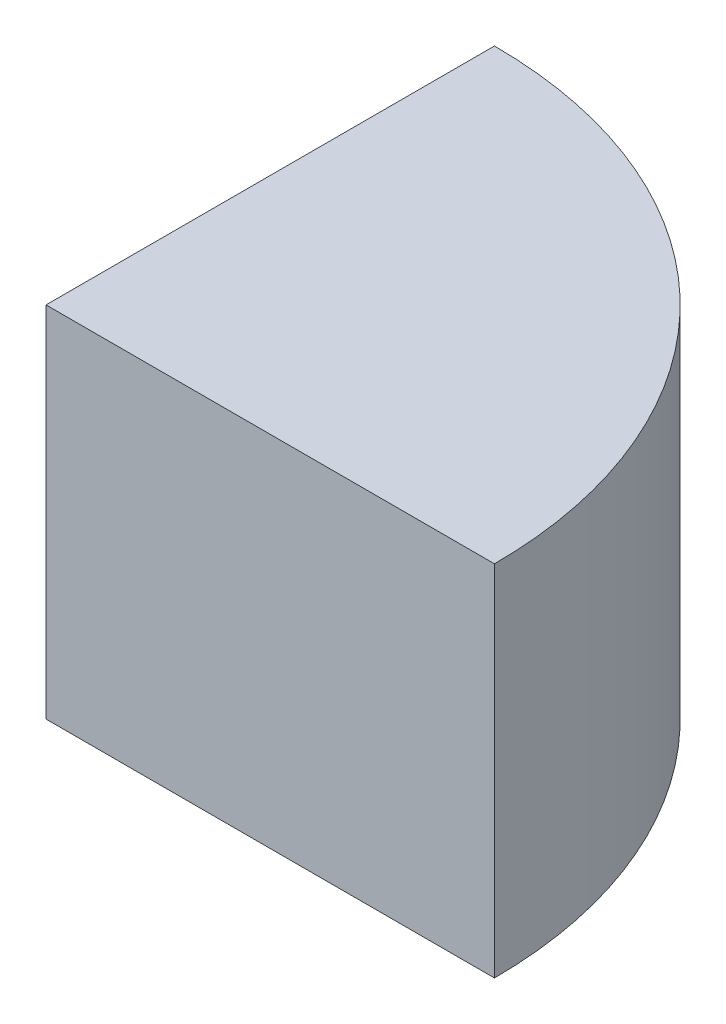
SolidWorks part; units mm, degrees
material "鎳"
ref_plane "前基準面" through (0, 0, 0) normal (0, 0, 1) x (1, 0, 0)
ref_plane "上基準面" through (0, 0, 0) normal (0, 1, 0) x (1, 0, 0)
ref_plane "右基準面" through (0, 0, 0) normal (1, 0, 0) x (0, 0, -1)
sketch "草圖1" plane through (0, 0, 0) normal (0, 1, 0) x (1, 0, 0)
  line L0 (0, 0) -> (0, 35)
  line L1 (0, 0) -> (35, 0)
  circle A0 centre (0, 0) radius 35
  point P4 (0, 0)
  point P6 (0, 0)
  dimension "D1" = 70
extrude "填料-伸長1" add sketch "草圖1" along normal blind 28 contours L1 A0 L0
sketch3d "URDF Reference"
  line L0 (0, 0, 0) -> (10, 0, 0) construction
  line L1 (0, 0, 0) -> (0, 0, -10) construction
  point P0 (0, 0, 0)
  point P1 (0, 0, 0)
